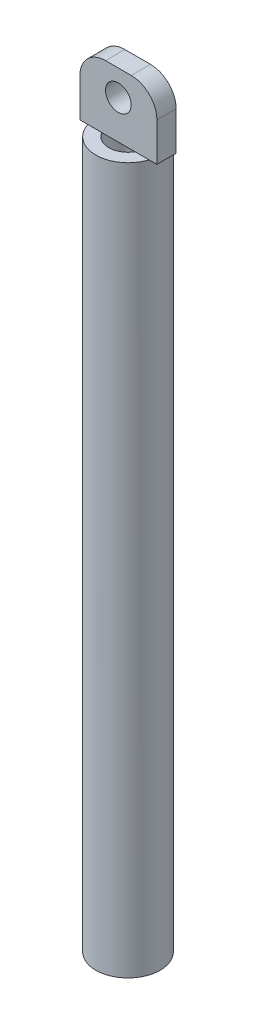
SolidWorks part; units mm, degrees
ref_plane "Front Plane" through (0, 0, 0) normal (0, 0, 1) x (1, 0, 0)
ref_plane "Top Plane" through (0, 0, 0) normal (0, 1, 0) x (1, 0, 0)
ref_plane "Right Plane" through (0, 0, 0) normal (1, 0, 0) x (0, 0, -1)
sketch "Sketch1" plane through (0, 0, 0) normal (0, 1, 0) x (1, 0, 0)
  circle A0 centre (0, 0) radius 1.5
  circle A1 centre (0, 0) radius 2.5
  dimension "D1" = 3
  dimension "D2" = 5
extrude "Boss-Extrude1" add sketch "Sketch1" along normal blind 55
sketch "Sketch2" plane through (0, 55, 0) normal (0, 1, 0) x (1, 0, 0)
  line L1 (-3, 0.75) -> (3, 0.75)
  line L2 (-3, 0.75) -> (-3, -0.75)
  line L3 (-3, -0.75) -> (3, -0.75)
  line L4 (3, 0.75) -> (3, -0.75)
  line L5 (-3, 0.75) -> (3, -0.75) construction
  line L6 (-3, -0.75) -> (3, 0.75) construction
  point P0 (0, 0)
  dimension "D1" = 1.5
  dimension "D2" = 6
extrude "Boss-Extrude2" add sketch "Sketch2" along normal blind 5
sketch "Sketch3" plane through (0, 0, -0.75) normal (0, 0, -1) x (-1, 0, 0)
  line L0 (-3, 60) -> (3, 60) construction
  circle A0 centre (0, 58) radius 1
  dimension "D1" = 2
  dimension "D2" = 2
extrude "Cut-Extrude1" cut sketch "Sketch3" against normal through all
fillet "Fillet1" radius 2 2 edges at (-3, 60, 0) (3, 60, 0)
